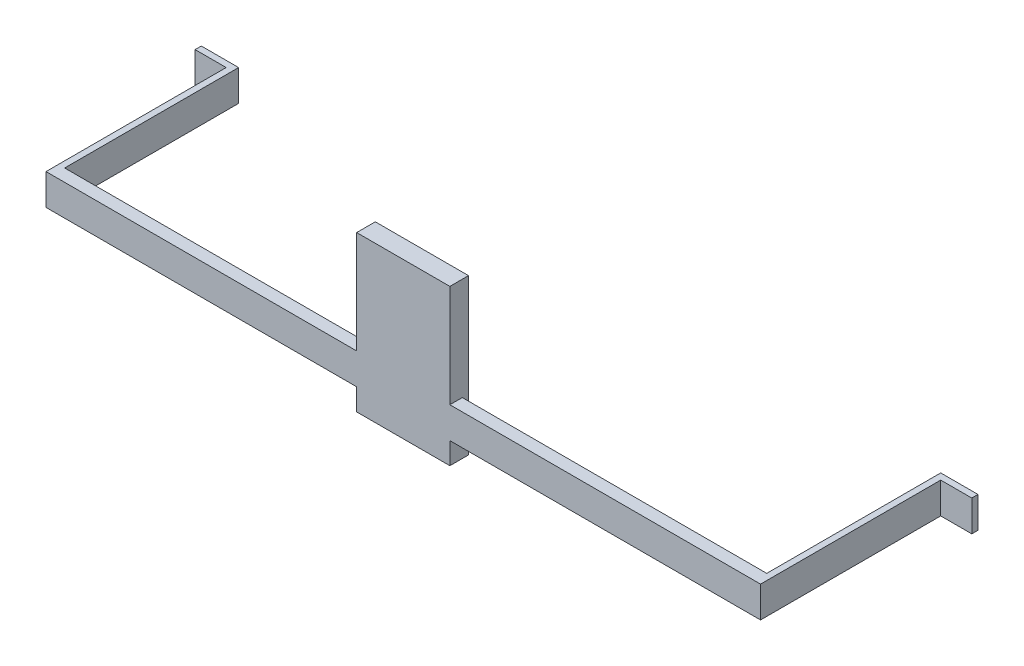
SolidWorks part; units mm, degrees
ref_plane "Front Plane" through (0, 0, 0) normal (0, 0, 1) x (1, 0, 0)
ref_plane "Top Plane" through (0, 0, 0) normal (0, 1, 0) x (1, 0, 0)
ref_plane "Right Plane" through (0, 0, 0) normal (1, 0, 0) x (0, 0, -1)
sketch "Sketch1" plane through (0, 0, 0) normal (0, 1, 0) x (1, 0, 0)
  line L0 (0, -55) -> (0, 55) construction
  line L1 (-57.5, -1) -> (57.5, -1)
  line L3 (-56.5, 1) -> (56.5, 1)
  line L8 (57.5, -1) -> (57.5, 28)
  line L11 (56.5, 29) -> (62.5, 29)
  line L13 (57.5, 28) -> (62.5, 28)
  line L14 (62.5, 29) -> (62.5, 28)
  line L15 (-57.5, -1) -> (-57.5, 28)
  line L16 (-62.5, 29) -> (-62.5, 28)
  line L17 (-57.5, 28) -> (-62.5, 28)
  line L19 (-56.5, 29) -> (-62.5, 29)
  line L20 (-56.5, 1) -> (-56.5, 29)
  line L22 (56.5, 1) -> (56.5, 29)
  point P0 (0, 0)
  dimension "D1" = 115
  dimension "D5" = 6
  dimension "D6" = 1
extrude "Boss-Extrude2" add sketch "Sketch1" along normal blind 5
sketch "Sketch3" plane through (0, 0, -1) normal (0, 0, -1) x (-1, 0, 0)
  line L0 (7.5, 21.5) -> (7.5, -3.5)
  line L5 (7.5, -3.5) -> (-7.5, -3.5)
  line L6 (6.5, 20.5) -> (-6.5, 20.5)
  line L7 (6.5, 20.5) -> (6.5, -2.5)
  line L8 (6.5, -2.5) -> (-6.5, -2.5)
  line L9 (-6.5, 20.5) -> (-6.5, -2.5)
  line L10 (-7.5, 21.5) -> (-7.5, -3.5)
  line L11 (7.5, 21.5) -> (-7.5, 21.5)
  point P9 (0, 1)
  point P15 (0, 0)
  dimension "D1" = 23
  dimension "D2" = 1
  dimension "D3" = 13
extrude "Boss-Extrude3" add sketch "Sketch3" along normal blind 1
sketch "Sketch5" plane through (0, 0, -1) normal (0, 0, 1) x (1, 0, 0)
  line L1 (-7.5, 21.5) -> (7.5, 21.5)
  line L2 (-7.5, 21.5) -> (-7.5, -3.5)
  line L3 (-7.5, -3.5) -> (7.5, -3.5)
  line L4 (7.5, 21.5) -> (7.5, -3.5)
extrude "Boss-Extrude5" add sketch "Sketch5" along normal up to surface (2 mm away) up to face at (0, 2.5, 1)
